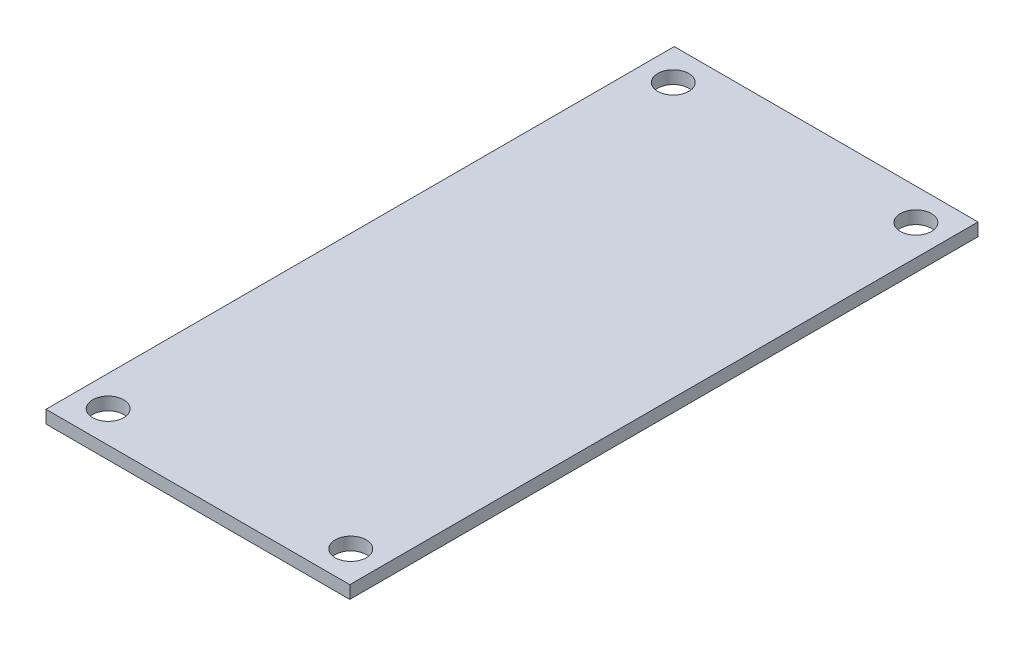
SolidWorks part; units mm, degrees
ref_plane "Alzado" through (0, 0, 0) normal (0, 0, 1) x (1, 0, 0)
ref_plane "Planta" through (0, 0, 0) normal (0, 1, 0) x (1, 0, 0)
ref_plane "Vista lateral" through (0, 0, 0) normal (1, 0, 0) x (0, 0, -1)
sketch "Sketch1" plane through (0, 0, 0) normal (0, 1, 0) x (1, 0, 0)
  line L0 (0, 0) -> (12.3, 0) construction
  line L1 (-15.4, -31.85) -> (15.4, -31.85)
  line L2 (-15.4, -31.85) -> (-15.4, 31.85)
  line L3 (-15.4, 31.85) -> (15.4, 31.85)
  line L4 (15.4, -31.85) -> (15.4, 31.85)
  line L5 (-15.4, -31.85) -> (15.4, 31.85) construction
  line L6 (-15.4, 31.85) -> (15.4, -31.85) construction
  line L7 (12.3, -28.65) -> (-12.3, -28.65) construction
  line L8 (12.3, -28.65) -> (12.3, 28.65) construction
  line L9 (12.3, 28.65) -> (-12.3, 28.65) construction
  line L10 (-12.3, -28.65) -> (-12.3, 28.65) construction
  line L11 (0, 0) -> (0, 28.65) construction
  circle A0 centre (12.3, 28.65) radius 1.575
  circle A1 centre (-12.3, 28.65) radius 1.575
  circle A2 centre (-12.3, -28.65) radius 1.575
  circle A3 centre (12.3, -28.65) radius 1.575
  point P0 (0, 0)
  point P6 (0, 0)
  dimension "D5" = 3.15
  dimension "D1" = 63.7
  dimension "D2" = 30.8
  dimension "D3" = 24.6
  dimension "D4" = 57.3
extrude "Boss-Extrude1" add sketch "Sketch1" along normal blind 1.3
